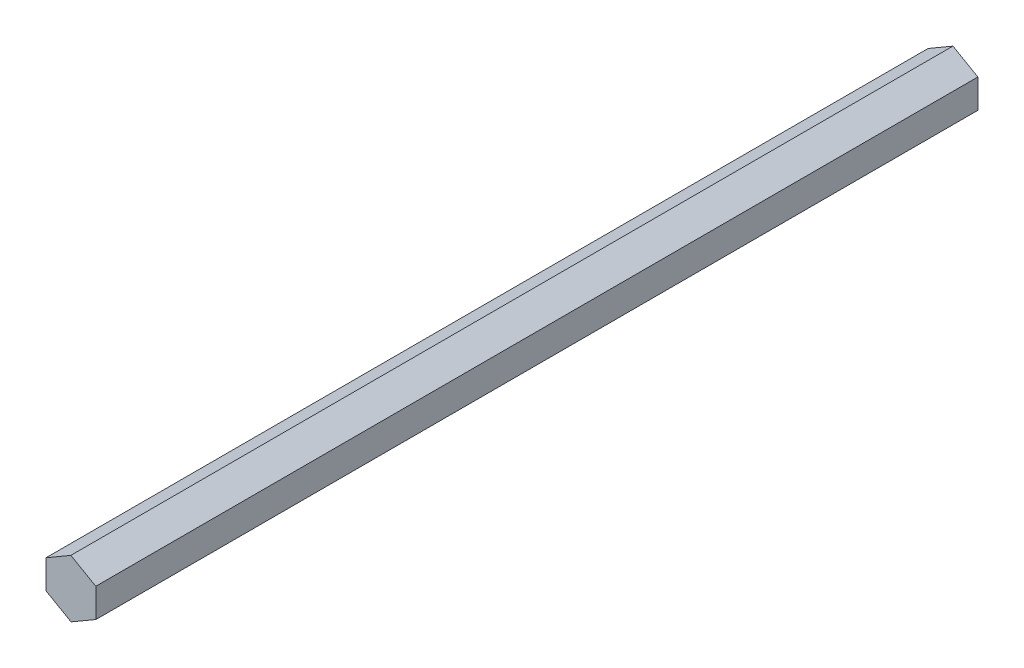
SolidWorks part; units mm, degrees
ref_plane "Front Plane" through (0, 0, 0) normal (0, 0, 1) x (1, 0, 0)
ref_plane "Top Plane" through (0, 0, 0) normal (0, 1, 0) x (1, 0, 0)
ref_plane "Right Plane" through (0, 0, 0) normal (1, 0, 0) x (0, 0, -1)
sketch "Sketch1" plane through (0, 0, 0) normal (0, 0, 1) x (1, 0, 0)
  line L1 (6.3338, 3.6941) -> (-0.0323, 7.3323)
  line L2 (-0.0323, 7.3323) -> (-6.3661, 3.6382)
  line L3 (-6.3661, 3.6382) -> (-6.3338, -3.6941)
  line L4 (-6.3338, -3.6941) -> (0.0323, -7.3323)
  line L5 (0.0323, -7.3323) -> (6.3661, -3.6382)
  line L6 (6.3661, -3.6382) -> (6.3338, 3.6941)
  circle A0 centre (0, 0) radius 6.35 construction
  dimension "D1" = 12.7
extrude "Boss-Extrude1" add sketch "Sketch1" along normal blind 225
